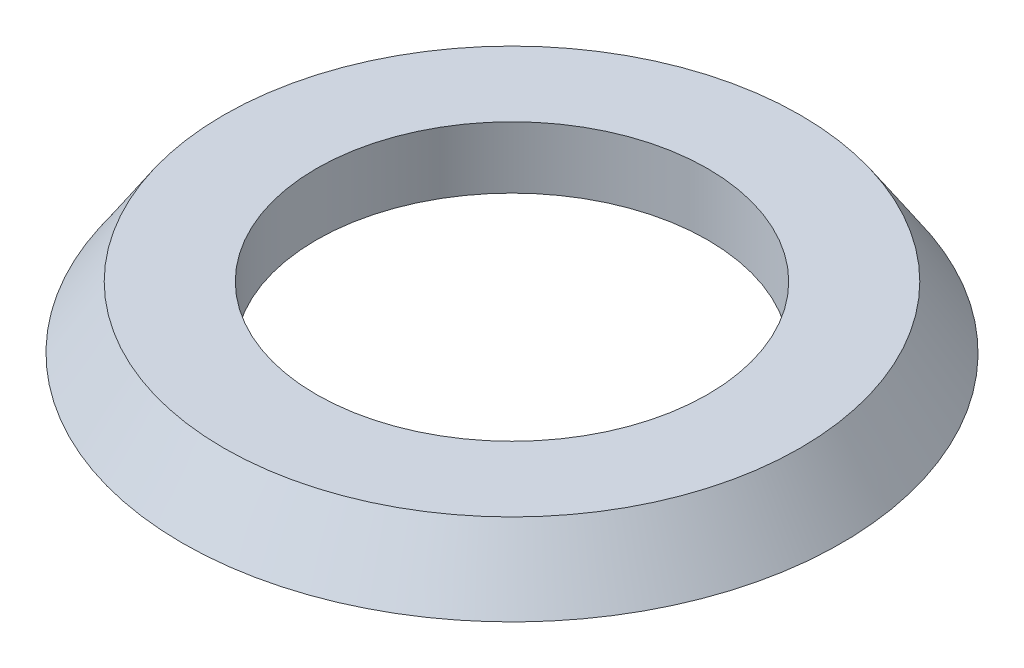
SolidWorks part; units mm, degrees
ref_plane "前视基准面" through (0, 0, 0) normal (0, 0, 1) x (1, 0, 0)
ref_plane "上视基准面" through (0, 0, 0) normal (0, 1, 0) x (1, 0, 0)
ref_plane "右视基准面" through (0, 0, 0) normal (1, 0, 0) x (0, 0, -1)
sketch "草图1" plane through (0, 0, 0) normal (0, 0, 1) x (1, 0, 0)
  line L0 (0, 0) -> (0, 3)
  line L1 (0, 0) -> (16, 0)
  line L2 (0, 3) -> (14, 3)
  line L3 (14, 3) -> (16, 0)
revolve "旋转1" add sketch "草图1" angle 360 about L0
sketch "草图2" plane through (0, 3, 0) normal (0, 1, 0) x (1, 0, 0)
  circle A0 centre (0, 0) radius 9.5
extrude "切除-拉伸1" cut sketch "草图2" against normal blind 10
